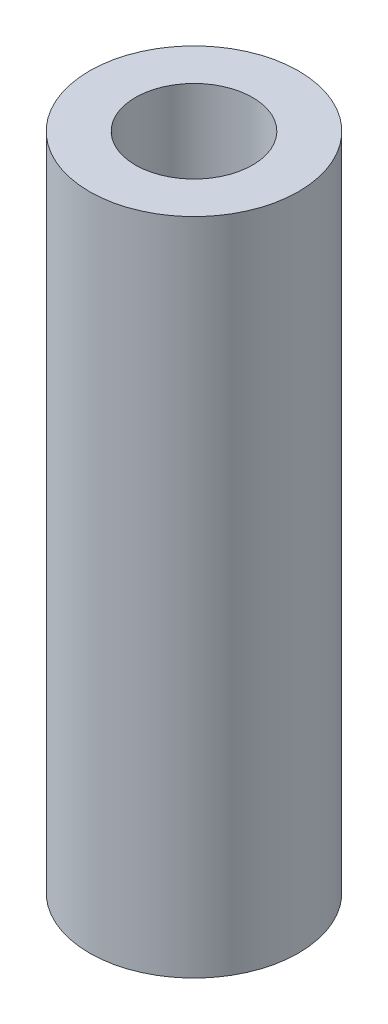
SolidWorks part; units mm, degrees
ref_plane "Front Plane" through (0, 0, 0) normal (0, 0, 1) x (1, 0, 0)
ref_plane "Top Plane" through (0, 0, 0) normal (0, 1, 0) x (1, 0, 0)
ref_plane "Right Plane" through (0, 0, 0) normal (1, 0, 0) x (0, 0, -1)
sketch "Sketch1" plane through (0, 0, 0) normal (0, 1, 0) x (1, 0, 0)
  circle A2 centre (0, 0) radius 3.2385
  circle A4 centre (0, 0) radius 5.7785
  dimension "D3" = 6.477
  dimension "D1" = 2.54
extrude "Boss-Extrude1" add sketch "Sketch1" along normal mid plane 36.449
